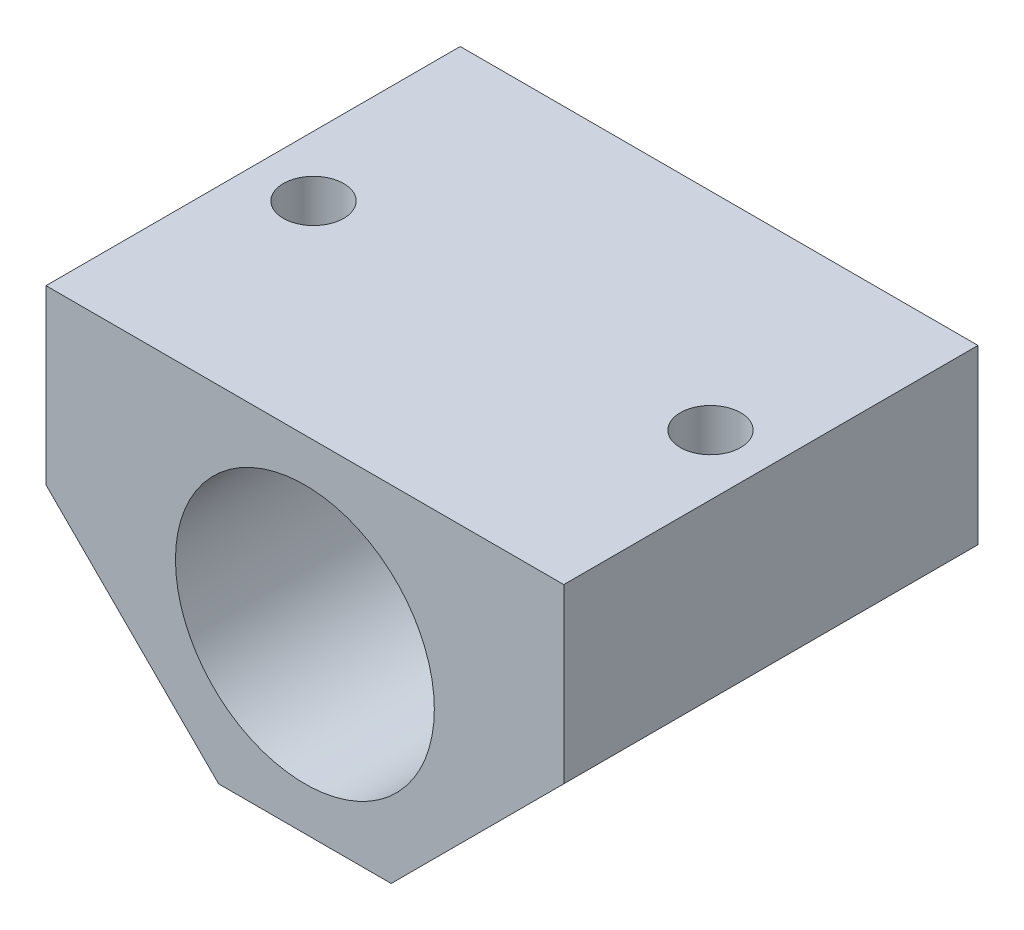
SolidWorks part; units mm, degrees
material "ABS PC"
ref_plane "Front Plane" through (0, 0, 0) normal (0, 0, 1) x (1, 0, 0)
ref_plane "Top Plane" through (0, 0, 0) normal (0, 1, 0) x (1, 0, 0)
ref_plane "Right Plane" through (0, 0, 0) normal (1, 0, 0) x (0, 0, -1)
sketch "Sketch1" plane through (0, 0, 0) normal (0, 0, 1) x (1, 0, 0)
  line L1 (0, 10) -> (0, 0)
  line L2 (0, 0) -> (-10, -10)
  line L3 (-10, -10) -> (-20, -10)
  line L4 (-20, -10) -> (-30, 0)
  line L5 (-30, 0) -> (-30, 10)
  line L6 (-30, 10) -> (0, 10)
  circle A0 centre (-15, 0) radius 7.5
  dimension "D5" = 15
  dimension "D6" = 15
  dimension "D1" = 30
  dimension "D2" = 10
  dimension "D3" = 10
  dimension "D4" = 10
  dimension "D7" = 10
extrude "Boss-Extrude1" add sketch "Sketch1" along normal blind 24
sketch "Sketch2" plane through (0, 10, 0) normal (0, 1, 0) x (1, 0, 0)
  line L0 (0, -24) -> (-30, -24) construction
  line L1 (0, -24) -> (0, 0) construction
  line L2 (-30, -24) -> (-30, 0) construction
  circle A0 centre (-26.5, -12) radius 1.75
  circle A1 centre (-3.5, -12) radius 1.75
  dimension "D1" = 3.5
  dimension "D3" = 3.5
  dimension "D2" = 12
  dimension "D4" = 3.5
extrude "Cut-Extrude1" cut sketch "Sketch2" against normal blind 24
sketch "Sketch4" plane through (0, 10, 0) normal (0, 1, 0) x (1, 0, 0)
  line L1 (-3.5, -15.1754) -> (-0.75, -13.5877)
  line L2 (-0.75, -13.5877) -> (-0.75, -10.4123)
  line L3 (-0.75, -10.4123) -> (-3.5, -8.8246)
  line L4 (-3.5, -8.8246) -> (-6.25, -10.4123)
  line L5 (-6.25, -10.4123) -> (-6.25, -13.5877)
  line L6 (-6.25, -13.5877) -> (-3.5, -15.1754)
  line L7 (-26.5, -15.1754) -> (-23.75, -13.5877)
  line L8 (-23.75, -13.5877) -> (-23.75, -10.4123)
  line L9 (-23.75, -10.4123) -> (-26.5, -8.8246)
  line L10 (-26.5, -8.8246) -> (-29.25, -10.4123)
  line L11 (-29.25, -10.4123) -> (-29.25, -13.5877)
  line L12 (-29.25, -13.5877) -> (-26.5, -15.1754)
  circle A0 centre (-3.5, -12) radius 2.75 construction
  circle A1 centre (-26.5, -12) radius 2.75 construction
  dimension "D1" = 5.5
extrude "Cut-Extrude2" cut sketch "Sketch4" against normal blind 7 from vertex at -10 starting at point (0, 0, 24)
